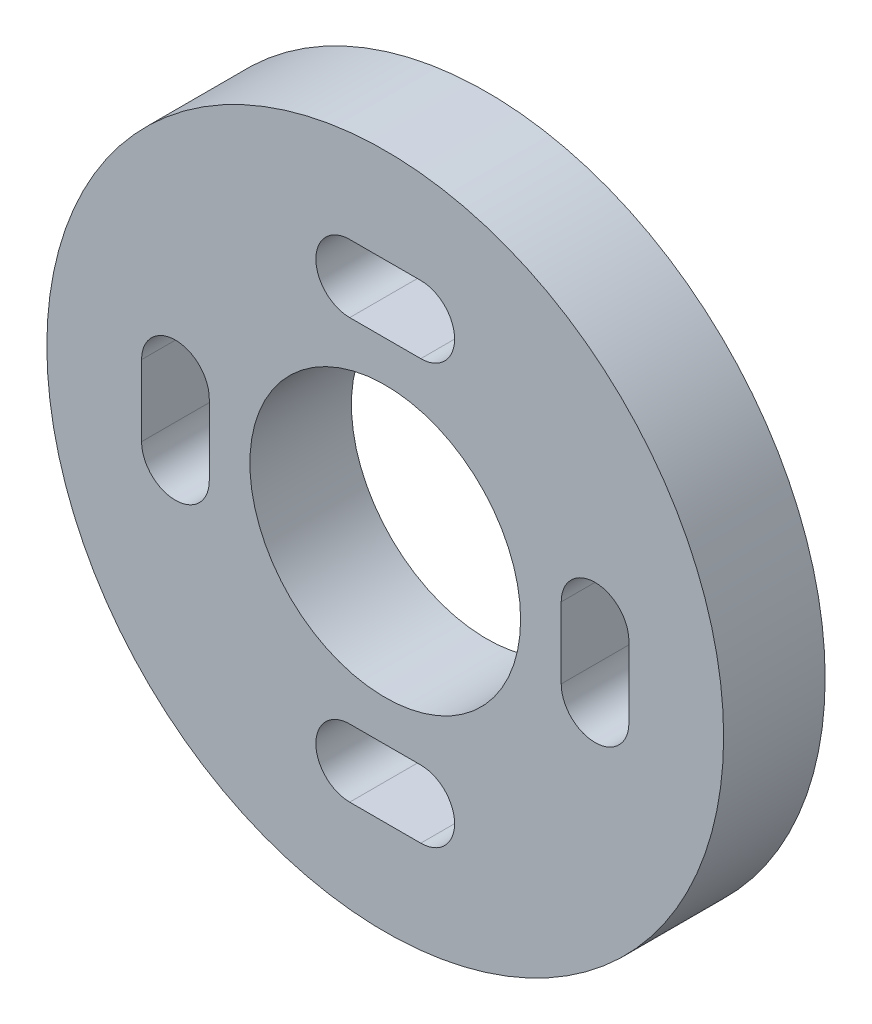
SolidWorks part; units mm, degrees
ref_plane "前基準面" through (0, 0, 0) normal (0, 0, 1) x (1, 0, 0)
ref_plane "上基準面" through (0, 0, 0) normal (0, 1, 0) x (1, 0, 0)
ref_plane "右基準面" through (0, 0, 0) normal (1, 0, 0) x (0, 0, -1)
sketch "草圖1" plane through (0, 0, 0) normal (0, 0, 1) x (1, 0, 0)
  circle A0 centre (0, 0) radius 10
  dimension "D1" = 20
extrude "填料-伸長1" add sketch "草圖1" along normal blind 3
sketch "草圖2" plane through (0, 0, 0) normal (0, 0, 1) x (1, 0, 0)
  line L0 (0, 4.1464) -> (0, -6.1002) construction
  line L1 (-8.1408, 0) -> (8.6618, 0) construction
  line L2 (-1.05, 6.2) -> (1.05, 6.2) construction
  line L3 (-1.05, 7.2) -> (1.05, 7.2)
  line L4 (-1.05, 5.2) -> (1.05, 5.2)
  line L5 (-6.2, 1.05) -> (-6.2, -1.05) construction
  line L6 (-5.2, 1.05) -> (-5.2, -1.05)
  line L7 (-7.2, 1.05) -> (-7.2, -1.05)
  line L8 (6.2, 1.05) -> (6.2, -1.05) construction
  line L9 (5.2, 1.05) -> (5.2, -1.05)
  line L10 (7.2, 1.05) -> (7.2, -1.05)
  line L11 (-1.05, -6.2) -> (1.05, -6.2) construction
  line L12 (-1.05, -7.2) -> (1.05, -7.2)
  line L13 (-1.05, -5.2) -> (1.05, -5.2)
  circle A0 centre (0, 0) radius 4
  arc A1 (-1.05, 7.2) -> (-1.05, 5.2) centre (-1.05, 6.2) ccw
  arc A2 (1.05, 5.2) -> (1.05, 7.2) centre (1.05, 6.2) ccw
  arc A3 (-5.2, 1.05) -> (-7.2, 1.05) centre (-6.2, 1.05) ccw
  arc A4 (-7.2, -1.05) -> (-5.2, -1.05) centre (-6.2, -1.05) ccw
  arc A5 (5.2, 1.05) -> (7.2, 1.05) centre (6.2, 1.05) cw
  arc A6 (7.2, -1.05) -> (5.2, -1.05) centre (6.2, -1.05) cw
  arc A7 (-1.05, -7.2) -> (-1.05, -5.2) centre (-1.05, -6.2) cw
  arc A8 (1.05, -5.2) -> (1.05, -7.2) centre (1.05, -6.2) cw
  point P9 (0, 6.2)
  point P14 (-6.2, 0)
  point P23 (6.2, 0)
  point P30 (0, -6.2)
  dimension "D1" = 8
  dimension "D2" = 2.1
  dimension "D3" = 1.05
  dimension "D4" = 2
  dimension "D5" = 2
  dimension "D6" = 2.1
  dimension "D7" = 1.05
  dimension "D8" = 6.2
  dimension "D9" = 6.2
extrude "除料-伸長1" cut sketch "草圖2" along normal blind 4
